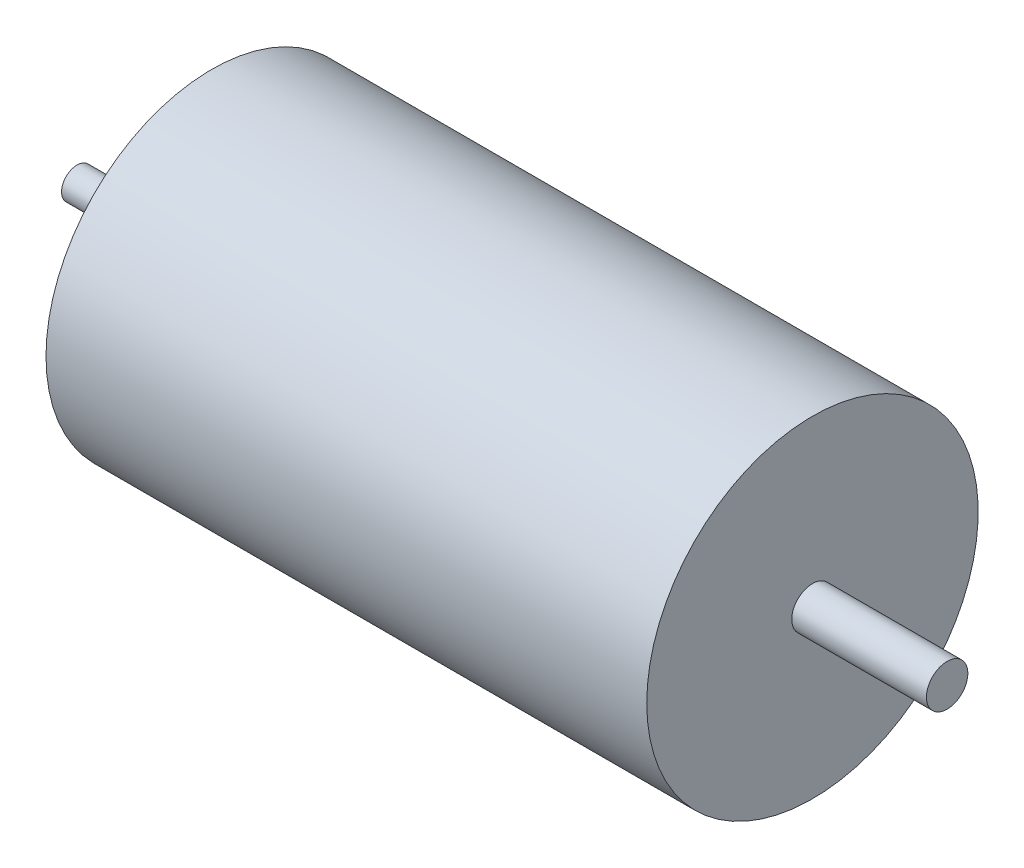
SolidWorks part; units mm, degrees
ref_plane "Plan de face" through (0, 0, 0) normal (0, 0, 1) x (1, 0, 0)
ref_plane "Plan de dessus" through (0, 0, 0) normal (0, 1, 0) x (1, 0, 0)
ref_plane "Plan de droite" through (0, 0, 0) normal (1, 0, 0) x (0, 0, -1)
sketch "Esquisse1" plane through (0, 0, 0) normal (0, 0, 1) x (1, 0, 0)
  line L0 (-42.4704, 0) -> (102.4592, 0) construction
  line L1 (0, 16) -> (58, 16)
  line L2 (58, 16) -> (58, 2)
  line L3 (58, 2) -> (71, 2)
  line L4 (71, 2) -> (71, 0)
  line L5 (71, 0) -> (-13, 0)
  line L6 (-13, 0) -> (-13, 1.5)
  line L7 (-13, 1.5) -> (-3, 1.5)
  line L8 (-3, 1.5) -> (-3, 6.5)
  line L9 (-3, 6.5) -> (0, 6.5)
  line L10 (0, 6.5) -> (0, 16)
  dimension "D1" = 32
  dimension "D2" = 4
  dimension "D3" = 3
  dimension "D4" = 3
  dimension "D5" = 13
  dimension "D6" = 13
  dimension "D7" = 13
  dimension "D8" = 58
revolve "Révolution1" add sketch "Esquisse1" angle 360 about L0
hole_wizard "Trou taraudé M2.5x0.451" positions "Esquisse3" profile "Esquisse2" tap size "M2.5x0.45" standard "Ansi Metric"
sketch "Esquisse3" plane through (0, 0, 0) normal (-1, 0, 0) x (0, 0, 1)
  line L0 (-8.2272, -4.75) -> (8.2272, -4.75) construction
  line L1 (8.2272, -4.75) -> (0, 9.5) construction
  line L2 (0, 9.5) -> (-8.2272, -4.75) construction
  circle A0 centre (0, 0) radius 9.5 construction
  point P0 (0, 9.5)
  point P2 (-8.2272, -4.75)
  point P4 (8.2272, -4.75)
  point P6 (0, -9.5)
  dimension "D1" = 19
sketch "Esquisse2" plane through (0, 9.5, 0) normal (0, 1, 0) x (0, 0, 1)
  line L0 (0, 0) -> (0, 7.8659)
  line L1 (0, 7.8659) -> (1.025, 7.25)
  line L2 (1.025, 7.25) -> (1.025, 0.25)
  line L3 (1.025, 0.25) -> (1.275, 0)
  line L5 (1.275, 0) -> (0, 0)
  line L6 (-1.025, 0.25) -> (-1.275, 0) construction
  line L10 (0, 7.8659) -> (-1.025, 7.25) construction
  line L11 (0, -6.35) -> (0, 107.95) construction
  dimension "Diamètre du trou pour taraudage" = 2.05
  dimension "Profondeur du trou pour taraudage" = 7.25
  dimension "Diamètre du fraisage entrant" = 2.55
  dimension "Angle du fraisage entrant" = 90
  dimension "Angle de pointe" = 118
cosmetic thread "Filetage de perçage1" parameters "D1"=5, "D2"=2.5
cosmetic thread "Filetage de perçage2" parameters "D1"=5, "D2"=2.5
cosmetic thread "Filetage de perçage3" parameters "D1"=5, "D2"=2.5
cosmetic thread "Filetage de perçage4" parameters "D1"=5, "D2"=2.5
